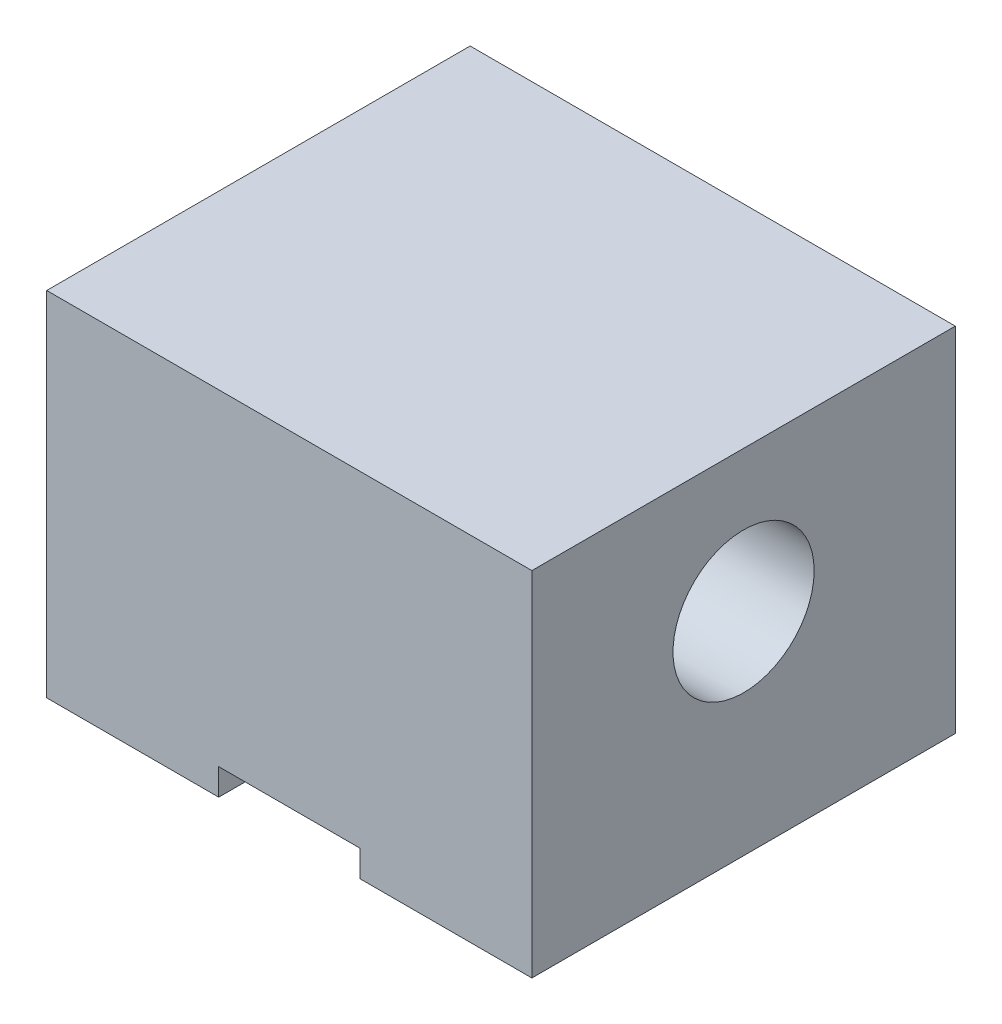
SolidWorks part; units mm, degrees
material "Oak"
ref_plane "Front Plane" through (0, 0, 0) normal (0, 0, 1) x (1, 0, 0)
ref_plane "Top Plane" through (0, 0, 0) normal (0, 1, 0) x (1, 0, 0)
ref_plane "Right Plane" through (0, 0, 0) normal (1, 0, 0) x (0, 0, -1)
other "Configuration Table"
sketch "Sketch1" plane through (0, 0, 0) normal (0, 1, 0) x (1, 0, 0)
  line L1 (-43.6562, 38.1) -> (43.6562, 38.1)
  line L2 (-43.6562, 38.1) -> (-43.6562, -38.1)
  line L3 (-43.6562, -38.1) -> (43.6563, -38.1)
  line L4 (43.6562, 38.1) -> (43.6563, -38.1)
  line L5 (-43.6562, 38.1) -> (43.6563, -38.1) construction
  line L6 (-43.6562, -38.1) -> (43.6562, 38.1) construction
  point P0 (0, 0)
  dimension "D1" = 76.2
  dimension "D2" = 87.3125
extrude "Boss-Extrude1" add sketch "Sketch1" along normal blind 63.5
sketch "Sketch2" plane through (0, 0, 0) normal (0, -1, 0) x (1, 0, 0)
  line L0 (-12.7, 38.1) -> (-12.7, -38.1)
  line L1 (-43.6562, 38.1) -> (43.6563, 38.1) construction
  line L2 (43.6562, -38.1) -> (-43.6562, -38.1) construction
  line L3 (-12.7, -38.1) -> (12.7, -38.1)
  line L4 (12.7, -38.1) -> (12.7, 38.1)
  line L5 (12.7, 38.1) -> (-12.7, 38.1)
  dimension "D1" = 25.4
  dimension "D2" = 12.7
extrude "Cut-Extrude1" cut sketch "Sketch2" against normal blind 4.7625
sketch "Sketch3" plane through (43.6563, 0, 0) normal (1, 0, 0) x (0, 0, -1)
  line L0 (-38.1, 0) -> (38.1, 0) construction
  line L3 (-38.1, 63.5) -> (-38.1, 0) construction
  circle A0 centre (0, 38.1) radius 12.7
  dimension "D1" = 25.4
  dimension "D2" = 38.1
  dimension "D3" = 38.1
extrude "Cut-Extrude2" cut sketch "Sketch3" against normal through all
